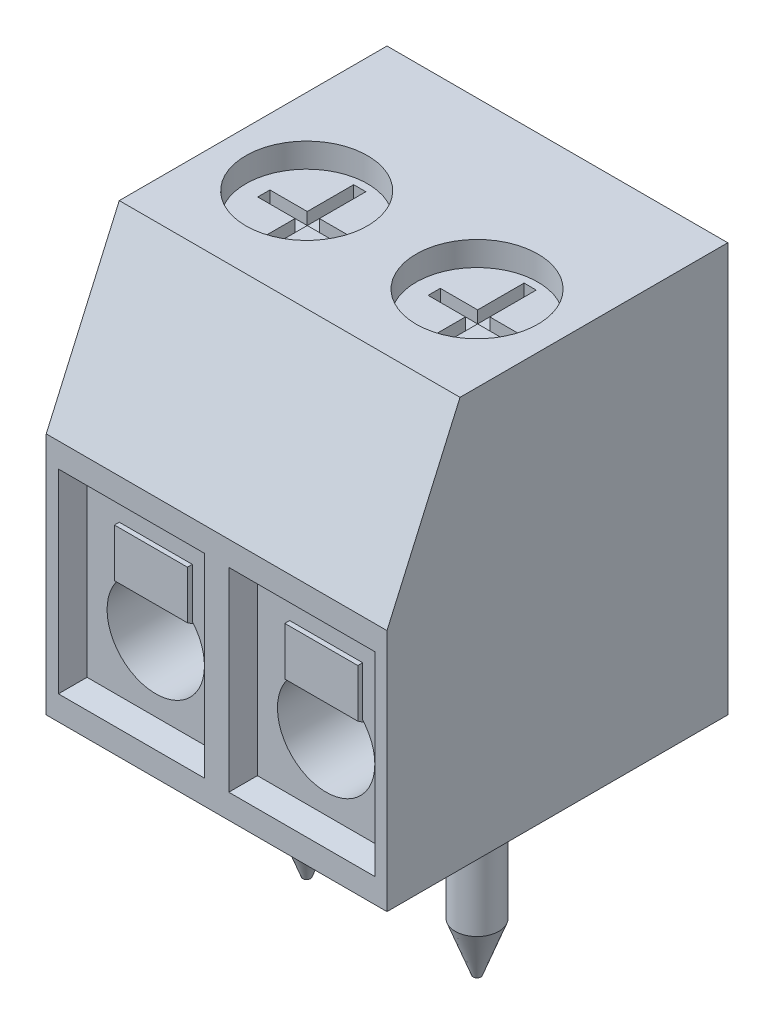
SolidWorks part; units mm, degrees
ref_plane "Front Plane" through (0, 0, 0) normal (0, 0, 1) x (1, 0, 0)
ref_plane "Top Plane" through (0, 0, 0) normal (0, 1, 0) x (1, 0, 0)
ref_plane "Right Plane" through (0, 0, 0) normal (1, 0, 0) x (0, 0, -1)
sketch "Sketch1" plane through (0, 0, 0) normal (1, 0, 0) x (0, 0, -1)
  line L0 (0, 5) -> (1.5, 8.4)
  line L1 (0, 0) -> (7, 0)
  line L2 (0, 0) -> (0, 5)
  line L3 (1.5, 8.4) -> (7, 8.4)
  line L4 (7, 0) -> (7, 8.4)
  dimension "D1" = 7
  dimension "D2" = 8.4
  dimension "D3" = 5
  dimension "D4" = 5.5
extrude "Boss-Extrude1" add sketch "Sketch1" along normal blind 7 contours L0 L3 L4 L1 L2
sketch "Sketch2" plane through (0, 8.4, 0) normal (0, 1, 0) x (1, 0, 0)
  line L0 (7, 7) -> (0, 7) construction
  line L1 (0, 1.5) -> (0, 7) construction
  circle A0 centre (1.75, 3.6) radius 1.25
  dimension "D1" = 2.5
  dimension "D2" = 3.4
  dimension "D3" = 1.75
extrude "Cut-Extrude1" cut sketch "Sketch2" against normal blind 0.5
sketch "Sketch3" plane through (0, 0, 0) normal (0, 0, 1) x (1, 0, 0)
  line L0 (0, 0) -> (0, 5) construction
  line L1 (0.25, 0.5) -> (3.25, 0.5)
  line L2 (0.25, 0.5) -> (0.25, 4.5)
  line L3 (0.25, 4.5) -> (3.25, 4.5)
  line L4 (3.25, 0.5) -> (3.25, 4.5)
  line L5 (7, 0) -> (0, 0) construction
  line L6 (7, 5) -> (0, 5) construction
  dimension "D1" = 0.25
  dimension "D2" = 3
  dimension "D3" = 0.5
  dimension "D4" = 0.5
extrude "Cut-Extrude2" cut sketch "Sketch3" against normal blind 0.5 draft 10 contours L3 L4 L1 L2
sketch "Sketch4" plane through (0, 0, -0.5) normal (0, 0, 1) x (1, 0, 0)
  line L0 (1.75, 0.5882) -> (1.75, 4.4118) construction
  line L1 (0.3382, 0.5882) -> (3.1618, 0.5882) construction
  line L2 (0.3382, 4.4118) -> (3.1618, 4.4118) construction
  line L3 (0.25, 0.5) -> (3.25, 0.5) construction
  circle A0 centre (1.75, 2) radius 1
  point P8 (1.75, 0.5)
  dimension "D1" = 2
  dimension "D2" = 1.5
extrude "Cut-Extrude3" cut sketch "Sketch4" against normal blind 6
ref_plane "Plane1" through (1.75, 0, 0) normal (1, 0, 0) x (0, 0, -1)
sketch "Sketch6" plane through (0, 0, 0) normal (0, -1, 0) x (1, 0, 0)
  line L0 (1.75, -3.85) -> (1.75, 3.85) construction
  line L1 (7, -7) -> (0, -7) construction
  circle A0 centre (1.75, -3.6) radius 0.45
  dimension "D1" = 0.9
  dimension "D2" = 3.4
extrude "Boss-Extrude3" add sketch "Sketch6" along normal blind 3.8
chamfer "Chamfer1" distance 1 angle 20.4 1 edges at (1.75, -3.8, -4.05)
sketch "Sketch7" plane through (1.75, 0, 0) normal (1, 0, 0) x (0, 0, -1)
  line L0 (0.5, 3.6787) -> (0.5, 2.7432)
  line L1 (0.5, 0.5882) -> (0.5, 4.4118) construction
  line L2 (0.5, 2.7432) -> (1.8997, 1.8322)
  line L3 (1.8997, 1.8322) -> (5.8881, 1.4383)
extrude "Extrude-Thin1" add sketch "Sketch7" along normal mid plane 1.5 thin
sketch "Sketch8" plane through (0, 7.9, 0) normal (0, 1, 0) x (1, 0, 0)
  line L0 (1.75, 4.6908) -> (1.75, 2.5325)
  line L1 (1.75, -3.85) -> (1.75, 3.85) construction
  line L2 (0.858, 3.6116) -> (2.7323, 3.6116)
  point P6 (0, 0)
extrude "Cut-Extrude-Thin1" cut sketch "Sketch8" against normal mid plane 0.5 thin thin type mid plane wall 0.25
pattern_linear "LPattern1" count 2 spacing 3.5 along (1, 0, 0) of "Cut-Extrude1", "Cut-Extrude2", "Cut-Extrude3", "Boss-Extrude3", "Chamfer1", "Extrude-Thin1", "Cut-Extrude-Thin1"
